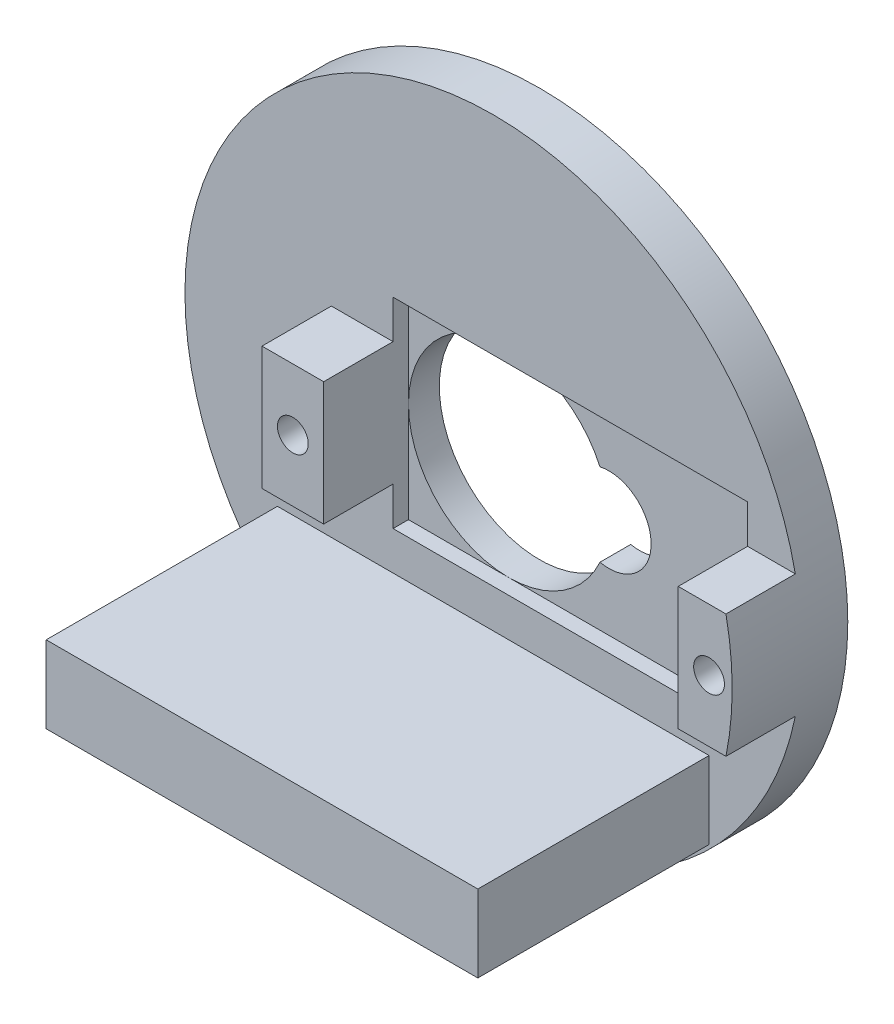
SolidWorks part; units mm, degrees
material "ABS"
ref_plane "Plano frontal" through (0, 0, 0) normal (0, 0, 1) x (1, 0, 0)
ref_plane "Plano superior" through (0, 0, 0) normal (0, 1, 0) x (1, 0, 0)
ref_plane "Plano direito" through (0, 0, 0) normal (1, 0, 0) x (0, 0, -1)
sketch "Esboço1" plane through (0, 0, 0) normal (0, 0, 1) x (1, 0, 0)
  circle A0 centre (0, 0) radius 20
  arc A1 (5.9214, 2.6809) -> (5.9214, -2.6809) centre (0, 0) ccw
  arc A2 (5.9214, -2.6809) -> (5.9214, 2.6809) centre (6.5, 0) ccw
extrude "Ressalto-extrusão1" add sketch "Esboço1" along normal blind 3
sketch "Esboço2" plane through (0, 0, 3) normal (0, 0, 1) x (1, 0, 0)
  line L0 (-6.5, 0) -> (-8.5, 0) construction
  line L2 (-10.5, -4) -> (-6.5, -4)
  line L3 (-10.5, -4) -> (-10.5, 4)
  line L4 (-10.5, 4) -> (-6.5, 4)
  line L5 (-6.5, -4) -> (-6.5, 4)
  line L6 (-8.5, 4) -> (-8.5, -4) construction
  line L7 (-10.5, 0) -> (-6.5, 0) construction
  line L9 (16.5, -4) -> (19.5959, -4)
  line L10 (16.5, -4) -> (16.5, 4)
  line L11 (16.5, 4) -> (19.5959, 4)
  line L13 (18.048, 4) -> (18.048, -4) construction
  line L14 (16.5, 0) -> (20.5, 0) construction
  arc A0 (5.9214, 2.6809) -> (5.9214, -2.6809) centre (0, 0) ccw construction
  circle A1 centre (-8.5, 0) radius 1
  circle A2 centre (18.5, 0) radius 1
  arc A3 (19.5959, -4) -> (19.5959, 4) centre (0, 0) ccw
  dimension "D1" = 2
  dimension "D3" = 27
  dimension "D2" = 8
extrude "Ressalto-extrusão3" add sketch "Esboço2" along normal blind 4.5
sketch "Esboço3" plane through (0, 0, 3) normal (0, 0, 1) x (1, 0, 0)
  line L1 (-6.5, -6.5) -> (16.5, -6.5)
  line L2 (-6.5, -6.5) -> (-6.5, 6.5)
  line L3 (-6.5, 6.5) -> (16.5, 6.5)
  line L4 (16.5, -6.5) -> (16.5, 6.5)
  line L5 (5, 6.5) -> (5, -6.5) construction
  line L6 (-8.5, 0) -> (18.5, 0) construction
  line L7 (-6.5, 0) -> (16.5, 0) construction
  point P0 (5, 0)
  point P4 (5.575, -2.4952)
  dimension "D1" = 23
extrude "Corte-extrusão1" cut sketch "Esboço3" against normal blind 1
sketch "Esboço4" plane through (0, 0, 3) normal (0, 0, 1) x (1, 0, 0)
  line L0 (0, 0) -> (0, -11.5) construction
  line L2 (-14, -14) -> (14, -14)
  line L3 (-14, -14) -> (-14, -9)
  line L4 (-14, -9) -> (14, -9)
  line L5 (14, -14) -> (14, -9)
  line L6 (0, -9) -> (0, -14) construction
  line L7 (-14, -11.5) -> (14, -11.5) construction
  dimension "D1" = 28
  dimension "D2" = 5
extrude "Ressalto-extrusão4" add sketch "Esboço4" along normal blind 15
